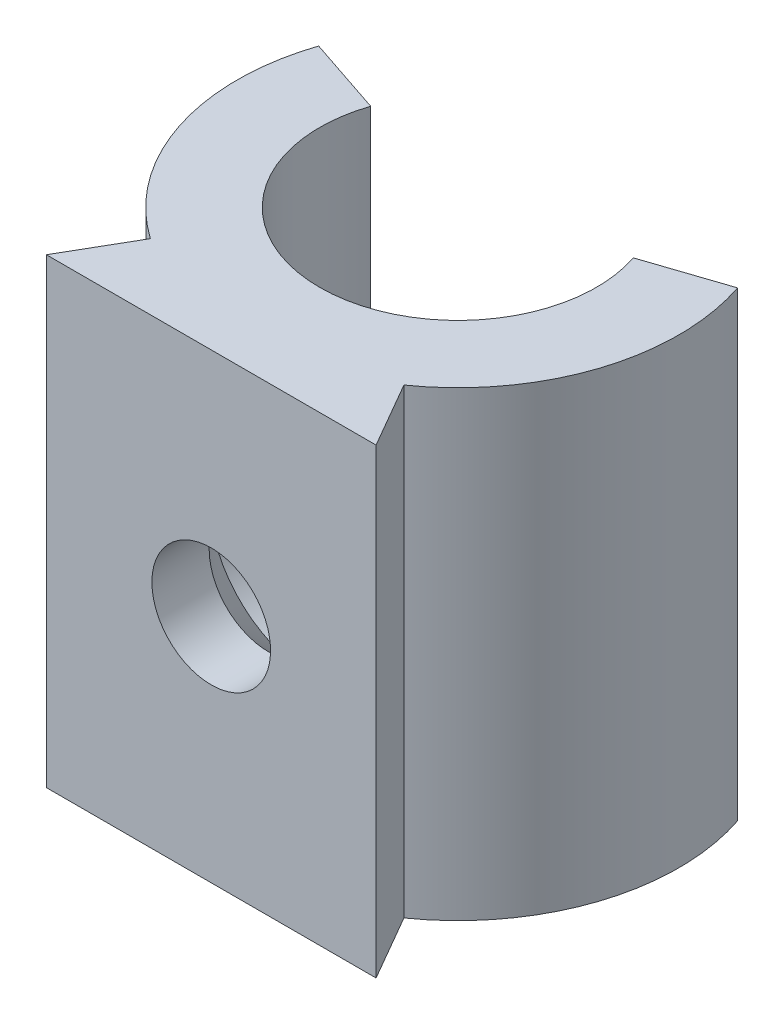
SolidWorks part; units mm, degrees
ref_plane "Front Plane" through (0, 0, 0) normal (0, 0, 1) x (1, 0, 0)
ref_plane "Top Plane" through (0, 0, 0) normal (0, 1, 0) x (1, 0, 0)
ref_plane "Right Plane" through (0, 0, 0) normal (1, 0, 0) x (0, 0, -1)
sketch "Sketch1" plane through (0, 0, 0) normal (0, 1, 0) x (1, 0, 0)
  line L0 (0, -1000) -> (0, 49000) construction
  line L1 (0, 0) -> (-6.3538, 2.1259)
  line L2 (0, 0) -> (6.3538, 2.1259)
  line L3 (-5, -7.4867) -> (5, -7.4867)
  line L4 (5, -7.4867) -> (3.8453, -5.4867)
  line L5 (-5, -7.4867) -> (-3.8453, -5.4867)
  circle A0 centre (0, 0) radius 4.2
  circle A1 centre (0, 0) radius 6.7
  point P12 (0, -7.4867)
  dimension "D1" = 8.4
  dimension "D3" = 143
  dimension "D4" = 2
  dimension "D5" = 10
  dimension "D6" = 60
  dimension "D2" = 2.5
extrude "Boss-Extrude1" add sketch "Sketch1" along normal blind 14 contours A1 L0 A0 L1 | L0 A1 L2 A0 | L0 L3 L4 A1 | L3 L0 A1 L5
ref_plane "Plane1" through (0, 0, 4.2) normal (0, 0, -1) x (-1, 0, 0)
sketch "Sketch4" plane through (0, 0, 4.2) normal (0, 0, -1) x (-1, 0, 0)
  line L2 (4.2, 14) -> (-4.2, 14) construction
  line L4 (4.2, 14) -> (-4.2, 14) construction
  line L5 (-4.2, 0) -> (4.2, 0) construction
  line L6 (-4.2, 0) -> (4.2, 0) construction
  line L7 (0, 14) -> (0, 0) construction
  circle A0 centre (0, 7) radius 3.25
  dimension "D1" = 6.5
extrude "Cut-Extrude1" cut sketch "Sketch4" along normal through all and the other way blind 0.2 contours A0
hole_wizard "CSK for M3 Flat Head Machine Screw4" positions "Sketch7" profile "Sketch8" countersink size "M3" standard "ANSI Metric"
sketch "Sketch7" plane through (0, 0, 4.4) normal (0, 0, -1) x (-1, 0, 0)
  point P0 (0, 7)
sketch "Sketch8" plane through (0, 7, 4.4) normal (1, 0, 0) x (0, 1, 0)
  line L0 (0, 0) -> (0, 8.5815)
  line L1 (0, 8.5815) -> (1.8, 7.5)
  line L2 (1.8, 7.5) -> (1.8, 1.35)
  line L3 (1.8, 1.35) -> (3.15, 0)
  line L5 (3.15, 0) -> (0, 0)
  line L6 (-1.8, 1.35) -> (-3.15, 0) construction
  line L10 (0, 8.5815) -> (-1.8, 7.5) construction
  line L11 (0, -6.35) -> (0, 107.95) construction
  dimension "Hole Dia." = 3.6
  dimension "Hole Depth" = 7.5
  dimension "Near C'Sink Dia." = 6.3
  dimension "Near C'Sink Angle" = 90
  dimension "Drill Angle" = 118
